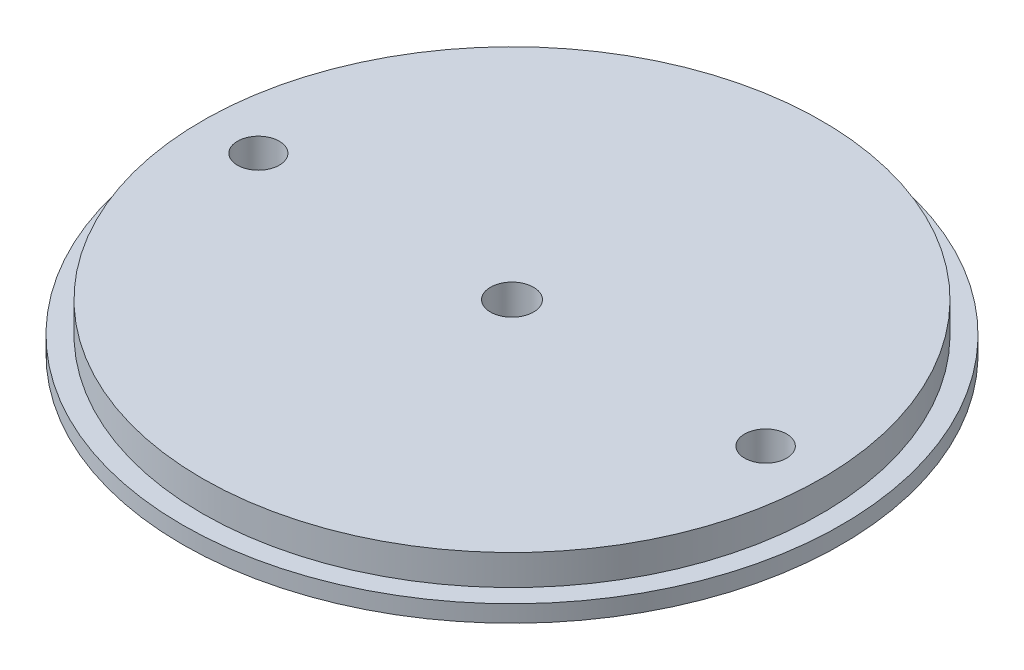
SolidWorks part; units mm, degrees
ref_plane "Front Plane" through (0, 0, 0) normal (0, 0, 1) x (1, 0, 0)
ref_plane "Top Plane" through (0, 0, 0) normal (0, 1, 0) x (1, 0, 0)
ref_plane "Right Plane" through (0, 0, 0) normal (1, 0, 0) x (0, 0, -1)
sketch "Sketch1" plane through (0, 0, 0) normal (0, 1, 0) x (1, 0, 0)
  circle A0 centre (0, 0) radius 50.4825
  dimension "D1" = 100.965
extrude "Boss-Extrude1" add sketch "Sketch1" along normal blind 2.5908
sketch "Sketch2" plane through (0, 2.5908, 0) normal (0, 1, 0) x (1, 0, 0)
  circle A0 centre (0, 0) radius 47.4472
  dimension "D1" = 94.8944
extrude "Boss-Extrude2" add sketch "Sketch2" along normal blind 4.6482 contours A0
sketch "Sketch3" plane through (0, 0, 0) normal (0, -1, 0) x (1, 0, 0)
  line L0 (-50.4825, 0) -> (50.4825, 0) construction
  circle A0 centre (0, 0) radius 50.4825 construction
  circle A1 centre (-38.852, 0) radius 3.2
  circle A2 centre (38.852, 0) radius 3.22
  circle A3 centre (0, 0) radius 3.302
  dimension "D1" = 6.4
  dimension "D2" = 6.44
  dimension "D3" = 6.604
  dimension "D4" = 38.852
  dimension "D5" = 38.852
extrude "Cut-Extrude1" cut sketch "Sketch3" against normal through all
